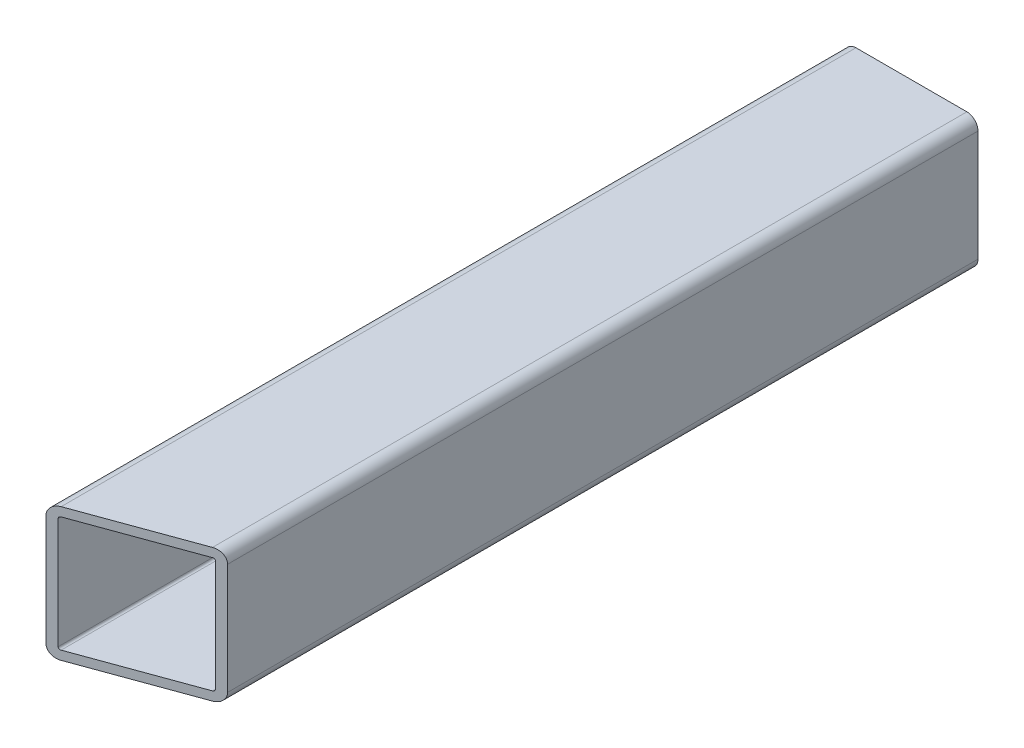
SolidWorks part; units mm, degrees
ref_plane "Front Plane" through (0, 0, 0) normal (0, 0, 1) x (1, 0, 0)
ref_plane "Top Plane" through (0, 0, 0) normal (0, 1, 0) x (1, 0, 0)
ref_plane "Right Plane" through (0, 0, 0) normal (1, 0, 0) x (0, 0, -1)
sketch "Sketch1" plane through (0, 0, 0) normal (0, 0, 1) x (1, 0, 0)
  line L1 (-15.875, 19.05) -> (15.875, 19.05)
  line L2 (-19.05, 15.875) -> (-19.05, -15.875)
  line L3 (-15.875, -19.05) -> (15.875, -19.05)
  line L4 (19.05, 15.875) -> (19.05, -15.875)
  line L5 (-19.05, 19.05) -> (19.05, -19.05) construction
  line L6 (-19.05, -19.05) -> (19.05, 19.05) construction
  arc A0 (-19.05, -15.875) -> (-15.875, -19.05) centre (-15.875, -15.875) ccw
  arc A1 (15.875, -19.05) -> (19.05, -15.875) centre (15.875, -15.875) ccw
  arc A2 (19.05, 15.875) -> (15.875, 19.05) centre (15.875, 15.875) ccw
  arc A3 (-15.875, 19.05) -> (-19.05, 15.875) centre (-15.875, 15.875) ccw
  point P0 (0, 0)
  dimension "D3" = 3.175
  dimension "D1" = 38.1
  dimension "D2" = 38.1
extrude "Extrude-Thin1" add sketch "Sketch1" along normal mid plane 228.6 thin
sketch "Sketch3" plane through (0, 19.05, 0) normal (0, 1, 0) x (1, 0, 0)
  line L0 (-19.05, -114.3) -> (19.05, -100.4327)
  line L3 (19.05, -114.3) -> (19.05, 114.3) construction
  line L4 (15.875, -114.3) -> (-15.875, -114.3) construction
  dimension "D1" = 20
extrude "Cut-Extrude1" cut sketch "Sketch3" against normal through all and the other way through all flip side to cut
